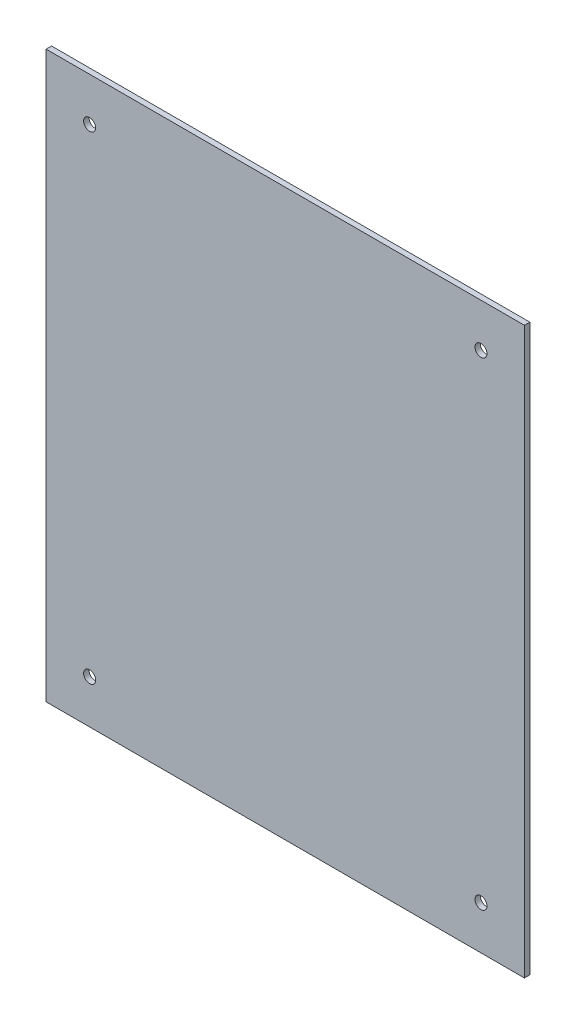
SolidWorks part; units mm, degrees
ref_plane "Front Plane" through (0, 0, 0) normal (0, 0, 1) x (1, 0, 0)
ref_plane "Top Plane" through (0, 0, 0) normal (0, 1, 0) x (1, 0, 0)
ref_plane "Right Plane" through (0, 0, 0) normal (1, 0, 0) x (0, 0, -1)
sketch "Sketch1" plane through (0, 0, 0) normal (0, 0, 1) x (1, 0, 0)
  line L1 (-139.7, -165.1) -> (139.7, -165.1)
  line L2 (-139.7, -165.1) -> (-139.7, 165.1)
  line L3 (-139.7, 165.1) -> (139.7, 165.1)
  line L4 (139.7, -165.1) -> (139.7, 165.1)
  line L5 (-139.7, -165.1) -> (139.7, 165.1) construction
  line L6 (-139.7, 165.1) -> (139.7, -165.1) construction
  line L7 (-114.3, -139.7) -> (114.3, -139.7) construction
  line L8 (-114.3, -139.7) -> (-114.3, 139.7) construction
  line L9 (-114.3, 139.7) -> (114.3, 139.7) construction
  line L10 (114.3, -139.7) -> (114.3, 139.7) construction
  line L11 (-114.3, -139.7) -> (114.3, 139.7) construction
  line L12 (-114.3, 139.7) -> (114.3, -139.7) construction
  circle A0 centre (-114.3, 139.7) radius 3.5
  circle A1 centre (114.3, 139.7) radius 3.5
  circle A2 centre (-114.3, -139.7) radius 3.5
  circle A3 centre (114.3, -139.7) radius 3.5
  point P0 (0, 0)
  point P6 (0, 0)
  dimension "D5" = 7
  dimension "D1" = 279.4
  dimension "D2" = 330.2
  dimension "D3" = 228.6
  dimension "D4" = 279.4
extrude "Boss-Extrude1" add sketch "Sketch1" along normal blind 3.175
